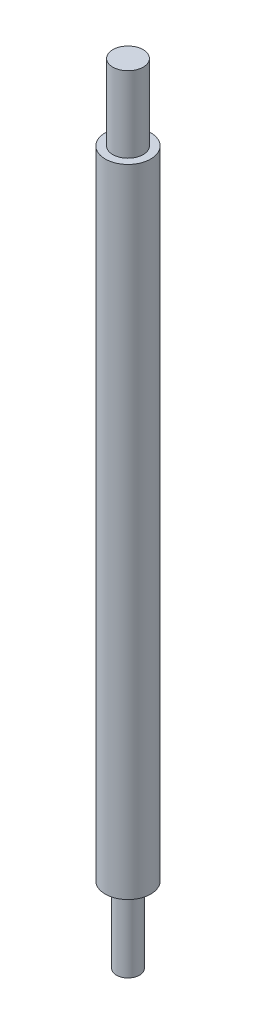
SolidWorks part; units mm, degrees
material "Cast Stainless Steel"
ref_plane "Front Plane" through (0, 0, 0) normal (0, 0, 1) x (1, 0, 0)
ref_plane "Top Plane" through (0, 0, 0) normal (0, 1, 0) x (1, 0, 0)
ref_plane "Right Plane" through (0, 0, 0) normal (1, 0, 0) x (0, 0, -1)
sketch "Sketch1" plane through (0, 0, 0) normal (0, 1, 0) x (1, 0, 0)
  circle A0 centre (0, 0) radius 3
  dimension "D1" = 6
extrude "Boss-Extrude2" add sketch "Sketch1" along normal blind 84
sketch "Sketch3" plane through (0, 84, 0) normal (0, 1, 0) x (1, 0, 0)
  circle A0 centre (0, 0) radius 2
  dimension "D1" = 4
extrude "Boss-Extrude3" add sketch "Sketch3" along normal blind 10
sketch "Sketch4" plane through (0, 0, 0) normal (0, -1, 0) x (1, 0, 0)
  circle A0 centre (0, 0) radius 1.526
extrude "Boss-Extrude4" add sketch "Sketch4" along normal blind 10
